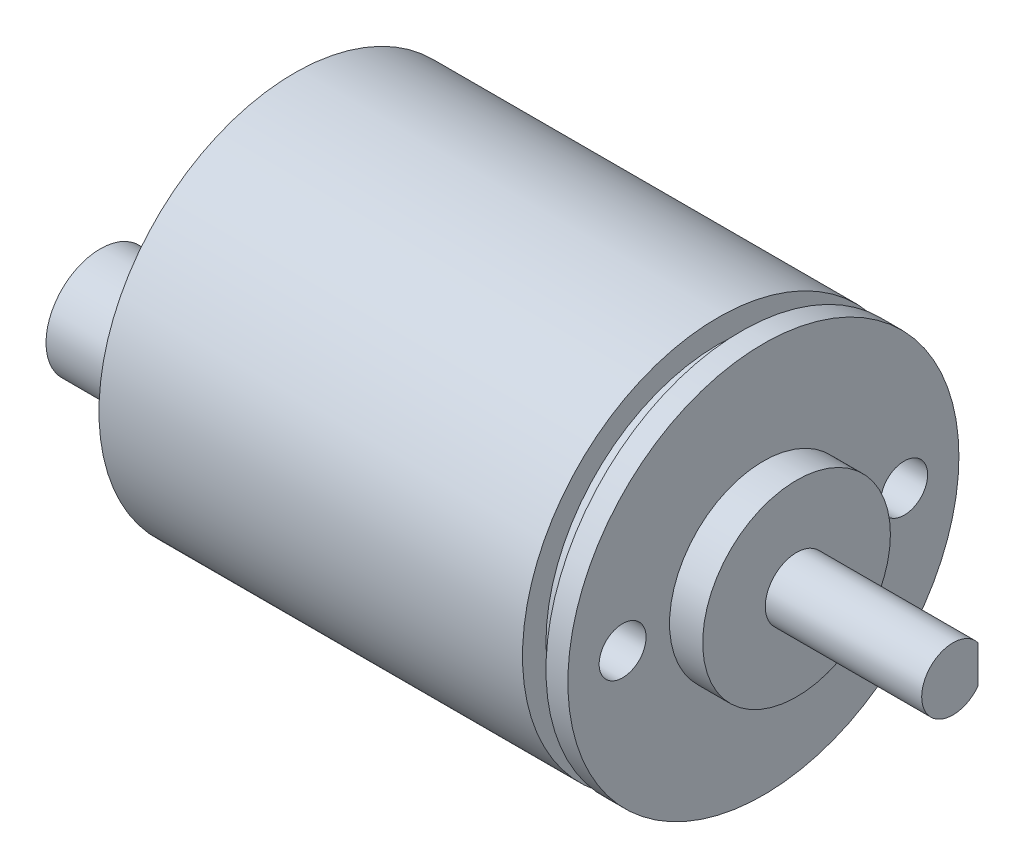
SolidWorks part; units mm, degrees
ref_plane "Front Plane" through (0, 0, 0) normal (0, 0, 1) x (1, 0, 0)
ref_plane "Top Plane" through (0, 0, 0) normal (0, 1, 0) x (1, 0, 0)
ref_plane "Right Plane" through (0, 0, 0) normal (1, 0, 0) x (0, 0, -1)
sketch "Sketch1" plane through (0, 0, 0) normal (1, 0, 0) x (0, 0, -1)
  circle A0 centre (0, 0) radius 12.5
  dimension "D1" = 25
extrude "Boss-Extrude1" add sketch "Sketch1" along normal blind 27.0764
sketch "Sketch2" plane through (27.0764, 0, 0) normal (1, 0, 0) x (0, 0, -1)
  circle A0 centre (0, 0) radius 11
  dimension "D1" = 22
extrude "Boss-Extrude2" add sketch "Sketch2" along normal blind 1.5
sketch "Sketch3" plane through (28.5764, 0, 0) normal (1, 0, 0) x (0, 0, -1)
  circle A0 centre (0, 0) radius 12.5
  dimension "D1" = 25
extrude "Boss-Extrude3" add sketch "Sketch3" along normal blind 1.4
sketch "Sketch4" plane through (29.9764, 0, 0) normal (1, 0, 0) x (0, 0, -1)
  circle A0 centre (0, 0) radius 6
  dimension "D1" = 12
extrude "Boss-Extrude4" add sketch "Sketch4" along normal blind 2.12
sketch "Sketch5" plane through (32.0964, 0, 0) normal (1, 0, 0) x (0, 0, -1)
  circle A0 centre (0, 0) radius 2
  dimension "D1" = 4
extrude "Boss-Extrude5" add sketch "Sketch5" along normal blind 10
sketch "Sketch6" plane through (42.0964, 0, 0) normal (1, 0, 0) x (0, 0, -1)
  line L1 (1.6, 3.2717) -> (4.2374, 3.2717)
  line L2 (1.6, 3.2717) -> (1.6, -3.3926)
  line L3 (1.6, -3.3926) -> (4.2374, -3.3926)
  line L4 (4.2374, 3.2717) -> (4.2374, -3.3926)
  circle A0 centre (0, 0) radius 2 construction
  dimension "D1" = 1.6
extrude "Cut-Extrude1" cut sketch "Sketch6" against normal blind 8
sketch "Sketch8" plane through (29.9764, 0, 0) normal (1, 0, 0) x (0, 0, -1)
  circle A0 centre (9, 0) radius 1.5
  circle A1 centre (0, 0) radius 6 construction
  circle A2 centre (-9, 0) radius 1.5
  dimension "D1" = 3
  dimension "D2" = 9
  dimension "D3" = 2
extrude "Cut-Extrude2" cut sketch "Sketch8" against normal blind 6.35
sketch "Sketch9" plane through (0, 0, 0) normal (-1, 0, 0) x (0, 0, 1)
  circle A0 centre (6.9146, 0) radius 3.4714
extrude "Boss-Extrude6" add sketch "Sketch9" along normal blind 5.5
